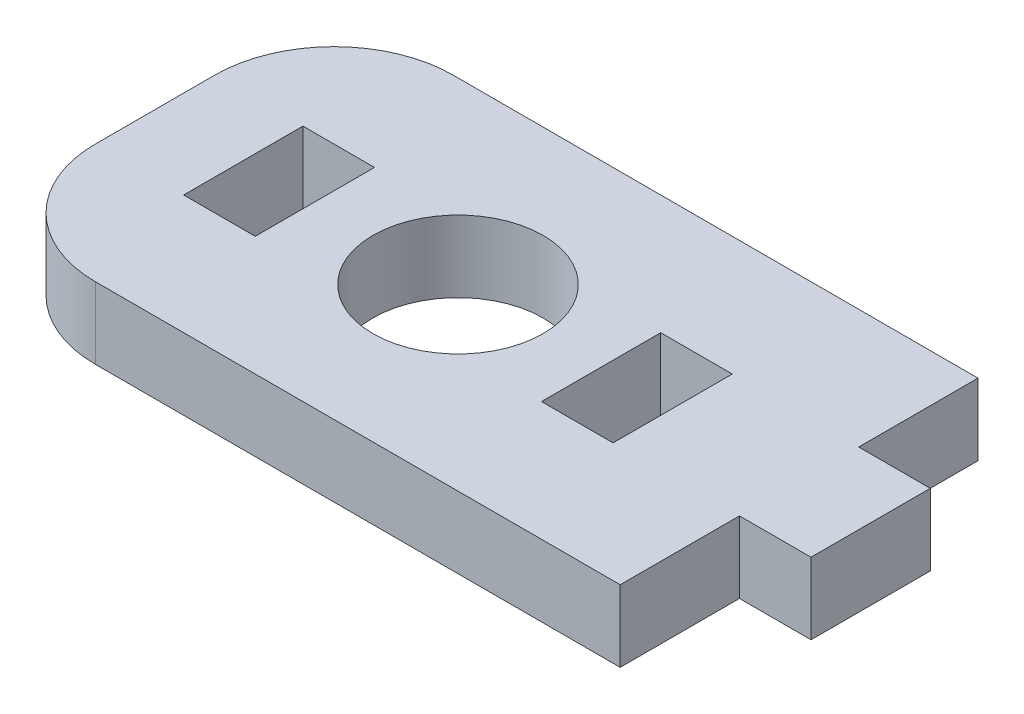
SolidWorks part; units mm, degrees
ref_plane "Front Plane" through (0, 0, 0) normal (0, 0, 1) x (1, 0, 0)
ref_plane "Top Plane" through (0, 0, 0) normal (0, 1, 0) x (1, 0, 0)
ref_plane "Right Plane" through (0, 0, 0) normal (1, 0, 0) x (0, 0, -1)
sketch "Sketch1" plane through (0, 0, 0) normal (0, 1, 0) x (1, 0, 0)
  line L0 (-21.8216, -5) -> (-21.8216, 10)
  line L1 (-21.8216, 10) -> (5.1784, 10)
  line L2 (5.1784, 10) -> (5.1784, 5)
  line L3 (5.1784, 5) -> (8.1784, 5)
  line L4 (8.1784, 5) -> (8.1784, 0)
  line L5 (8.1784, 0) -> (5.1784, 0)
  line L6 (5.1784, 0) -> (5.1784, -5)
  line L7 (5.1784, -5) -> (-21.8216, -5)
  line L8 (-21.8216, 2.5) -> (-16.6216, 2.5) construction
  line L9 (-16.6216, 2.5) -> (-9.1216, 2.5) construction
  line L10 (-15.1216, 5) -> (-18.1216, 5)
  line L11 (-15.1216, 5) -> (-15.1216, 0)
  line L12 (-15.1216, 0) -> (-18.1216, 0)
  line L13 (-18.1216, 5) -> (-18.1216, 0)
  line L14 (-15.1216, 5) -> (-18.1216, 0) construction
  line L15 (-15.1216, 0) -> (-18.1216, 5) construction
  line L16 (-9.1216, 2.5) -> (-9.1216, 50002.5) construction
  line L17 (-3.1216, 0) -> (-0.1216, 5) construction
  line L18 (-3.1216, 5) -> (-0.1216, 0) construction
  line L19 (-0.1216, 5) -> (-0.1216, 0)
  line L20 (-3.1216, 0) -> (-0.1216, 0)
  line L21 (-3.1216, 5) -> (-3.1216, 0)
  line L22 (-3.1216, 5) -> (-0.1216, 5)
  circle A0 centre (-9.1216, 2.5) radius 3.5685
  dimension "D8" = 7.137
  dimension "D1" = 3
  dimension "D2" = 5
  dimension "D3" = 5
  dimension "D4" = 27
  dimension "D5" = 5.2
  dimension "D6" = 3
  dimension "D7" = 5
  dimension "D9" = 7.5
extrude "Boss-Extrude1" add sketch "Sketch1" along normal blind 3
fillet "Fillet1" radius 5 2 edges at (-21.8216, 1.5, 5) (-21.8216, 1.5, -10)
